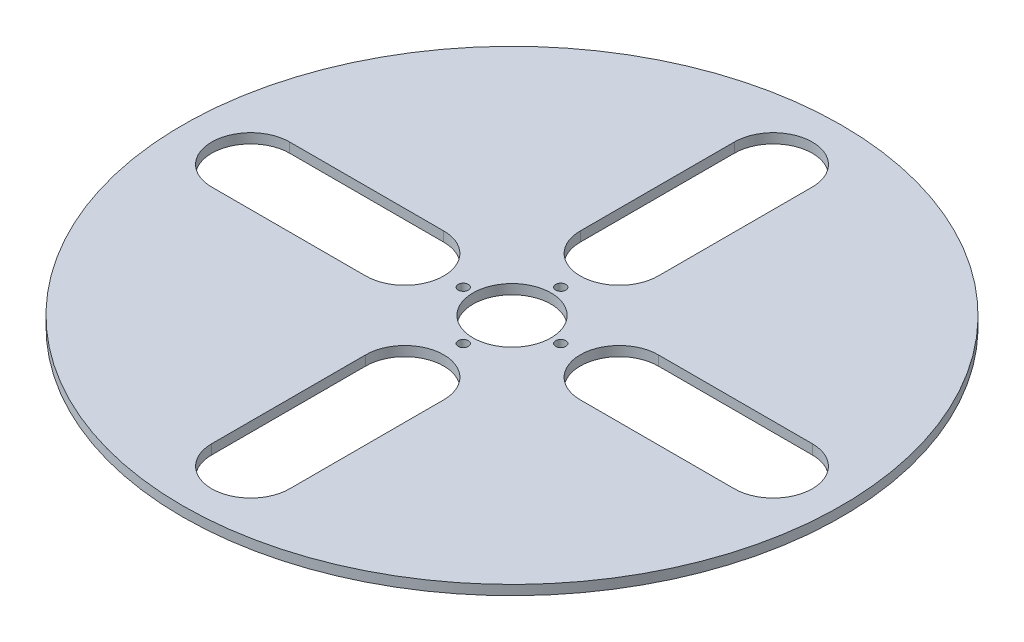
SolidWorks part; units mm, degrees
material "PC High Viscosity"
ref_plane "Front Plane" through (0, 0, 0) normal (0, 0, 1) x (1, 0, 0)
ref_plane "Top Plane" through (0, 0, 0) normal (0, 1, 0) x (1, 0, 0)
ref_plane "Right Plane" through (0, 0, 0) normal (1, 0, 0) x (0, 0, -1)
sketch "Sketch1" plane through (0, 0, 0) normal (0, 1, 0) x (1, 0, 0)
  line L0 (-55, 0) -> (55, 0) construction
  line L1 (7.3323, 0) -> (3.6662, 6.35)
  line L2 (3.6662, 6.35) -> (-3.6662, 6.35)
  line L3 (-3.6662, 6.35) -> (-7.3323, 0)
  line L4 (-7.3323, 0) -> (-3.6662, -6.35)
  line L5 (-3.6662, -6.35) -> (3.6662, -6.35)
  line L6 (3.6662, -6.35) -> (7.3323, 0)
  circle A4 centre (0, 0) radius 214.63
  circle A5 centre (0, 0) radius 6.35 construction
  circle A6 centre (0, 0) radius 25.4
  point P0 (0, 0)
  dimension "D1" = 12.7
  dimension "D2" = 50.8
  dimension "diameter" = 429.26
extrude "Boss-Extrude1" add sketch "Sketch1" along normal blind 6.35 contours A4 A6
sketch "Sketch3" plane through (0, 6.35, 0) normal (0, 1, 0) x (1, 0, 0)
  circle A0 centre (0, 31.75) radius 3.2893
  circle A1 centre (31.75, 0) radius 3.2893
  circle A2 centre (0, -31.75) radius 3.2893
  circle A3 centre (-31.75, 0) radius 3.2893
  point P12 (0, 0)
  dimension "D1" = 6.5786
  dimension "D2" = 31.75
  dimension "D3" = 4
extrude "Cut-Extrude2" cut sketch "Sketch3" against normal through all
sketch "Sketch4" plane through (0, 6.35, 0) normal (0, 1, 0) x (1, 0, 0)
  line L0 (-214.63, 0) -> (214.63, 0) construction
  line L1 (0, 214.63) -> (0, -214.63) construction
  line L2 (0, 170.18) -> (0, 69.85) construction
  line L3 (25.4, 170.18) -> (25.4, 69.85)
  line L4 (-25.4, 170.18) -> (-25.4, 69.85)
  line L7 (170.18, 0) -> (69.85, 0) construction
  line L10 (170.18, -25.4) -> (69.85, -25.4)
  line L13 (170.18, 25.4) -> (69.85, 25.4)
  line L14 (0, -170.18) -> (0, -69.85) construction
  line L15 (-25.4, -170.18) -> (-25.4, -69.85)
  line L16 (25.4, -170.18) -> (25.4, -69.85)
  line L17 (-170.18, 0) -> (-69.85, 0) construction
  line L18 (-170.18, 25.4) -> (-69.85, 25.4)
  line L19 (-170.18, -25.4) -> (-69.85, -25.4)
  circle A0 centre (0, 0) radius 214.63 construction
  arc A1 (25.4, 170.18) -> (-25.4, 170.18) centre (0, 170.18) ccw
  arc A2 (-25.4, 69.85) -> (25.4, 69.85) centre (0, 69.85) ccw
  arc A9 (170.18, -25.4) -> (170.18, 25.4) centre (170.18, 0) ccw
  arc A10 (69.85, 25.4) -> (69.85, -25.4) centre (69.85, 0) ccw
  arc A11 (-25.4, -170.18) -> (25.4, -170.18) centre (0, -170.18) ccw
  arc A12 (25.4, -69.85) -> (-25.4, -69.85) centre (0, -69.85) ccw
  arc A13 (-170.18, 25.4) -> (-170.18, -25.4) centre (-170.18, 0) ccw
  arc A14 (-69.85, -25.4) -> (-69.85, 25.4) centre (-69.85, 0) ccw
  point P9 (0, 120.015)
  point P20 (120.015, 0)
  point P27 (0, -120.015)
  point P34 (-120.015, 0)
  point P39 (0, -19.05)
  point P40 (0, 0)
  dimension "D3" = 25.4
  dimension "D1" = 44.45
  dimension "D2" = 69.85
  dimension "D4" = 4
extrude "Cut-Extrude3" cut sketch "Sketch4" against normal through all
